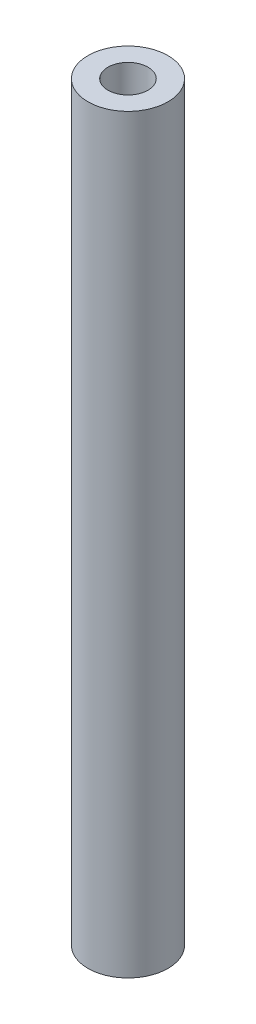
SolidWorks part; units mm, degrees
ref_plane "前基準面" through (0, 0, 0) normal (0, 0, 1) x (1, 0, 0)
ref_plane "上基準面" through (0, 0, 0) normal (0, 1, 0) x (1, 0, 0)
ref_plane "右基準面" through (0, 0, 0) normal (1, 0, 0) x (0, 0, -1)
sketch "草圖1" plane through (0, 0, 0) normal (0, 1, 0) x (1, 0, 0)
  circle A0 centre (0, 0) radius 4
  dimension "D1" = 8
extrude "填料-伸長1" add sketch "草圖1" along normal blind 75
sketch "草圖2" plane through (0, 75, 0) normal (0, 1, 0) x (1, 0, 0)
  circle A0 centre (0, 0) radius 2
extrude "除料-伸長1" cut sketch "草圖2" against normal blind 4
sketch "草圖3" plane through (0, 0, 0) normal (0, -1, 0) x (1, 0, 0)
  circle A0 centre (0, 0) radius 2
  dimension "D1" = 4
extrude "除料-伸長2" cut sketch "草圖3" against normal blind 4 contours A0
